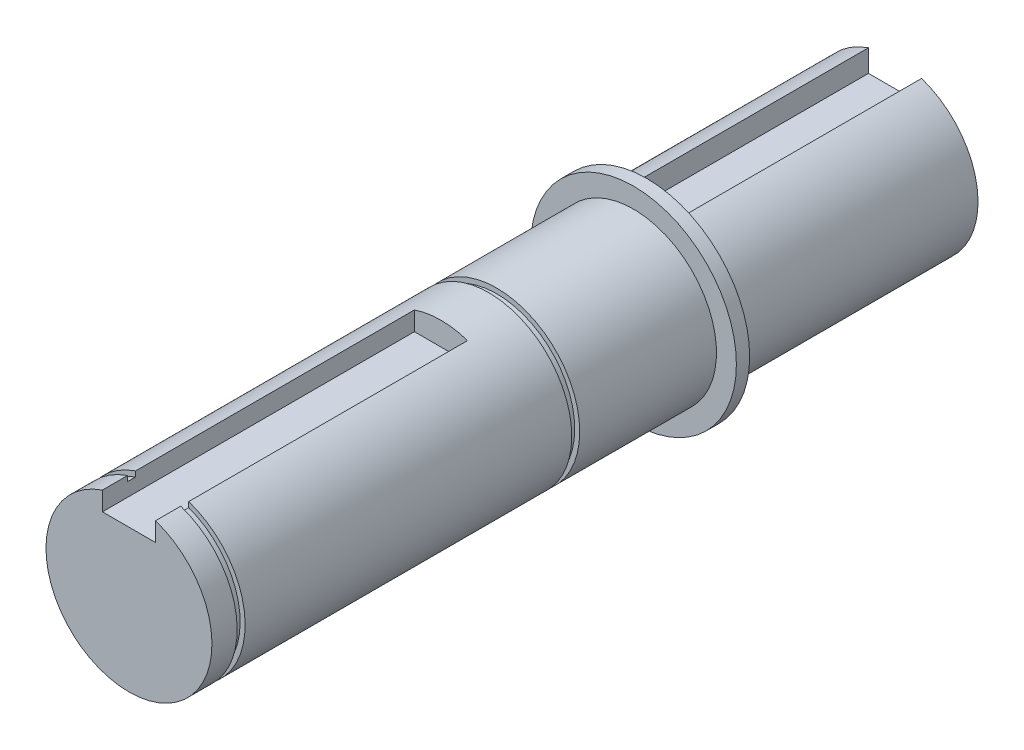
SolidWorks part; units mm, degrees
material "Plain Carbon Steel"
ref_plane "Front Plane" through (0, 0, 0) normal (0, 0, 1) x (1, 0, 0)
ref_plane "Top Plane" through (0, 0, 0) normal (0, 1, 0) x (1, 0, 0)
ref_plane "Right Plane" through (0, 0, 0) normal (1, 0, 0) x (0, 0, -1)
sketch "Sketch1" plane through (0, 0, 0) normal (0, 0, 1) x (1, 0, 0)
  circle A0 centre (0, 0) radius 12.5
  dimension "D1" = 25
extrude "Boss-Extrude1" add sketch "Sketch1" along normal blind 115.4
sketch "Sketch4" plane through (0, 0, 0) normal (0, 0, -1) x (-1, 0, 0)
  line L0 (0, 17.05) -> (0, -17.05) construction
  line L1 (-4, 8.5) -> (4, 8.5)
  line L2 (-4, 8.5) -> (-4, 16.5)
  line L3 (-4, 16.5) -> (4, 16.5)
  line L4 (4, 8.5) -> (4, 16.5)
  line L5 (-4, 8.5) -> (4, 16.5) construction
  line L6 (-4, 16.5) -> (4, 8.5) construction
  circle A0 centre (0, 0) radius 12.5 construction
  point P0 (0, 12.5)
  dimension "D1" = 8
  dimension "D2" = 8
extrude "Cut-Extrude1" cut sketch "Sketch4" against normal blind 35.4
ref_plane "Plane1" through (0, 0, 37.4) normal (0, 0, -1) x (-1, 0, 0)
sketch "Sketch11" plane through (0, 0, 37.4) normal (0, 0, -1) x (-1, 0, 0)
  circle A0 centre (0, 0) radius 15.5
  dimension "D1" = 31
extrude "Boss-Extrude4" add sketch "Sketch11" against normal blind 2
ref_plane "Plane2" through (0, 0, 60) normal (0, 0, 1) x (1, 0, 0)
sketch "Sketch12" plane through (0, 0, 60) normal (0, 0, 1) x (1, 0, 0)
  circle A0 centre (0, 0) radius 12.5
  circle A1 centre (0, 0) radius 11.75
  dimension "D1" = 25
  dimension "D2" = 23.5
extrude "Cut-Extrude2" cut sketch "Sketch12" along normal blind 1.2
sketch "Sketch13" plane through (0, 0, 115.4) normal (0, 0, 1) x (1, 0, 0)
  line L1 (-4, 9) -> (4, 9)
  line L2 (-4, 9) -> (-4, 16)
  line L3 (-4, 16) -> (4, 16)
  line L4 (4, 9) -> (4, 16)
  line L5 (-4, 9) -> (4, 16) construction
  line L6 (-4, 16) -> (4, 9) construction
  circle A0 centre (0, 0) radius 12.5 construction
  point P0 (0, 12.5)
  dimension "D1" = 8
  dimension "D2" = 7
extrude "Cut-Extrude3" cut sketch "Sketch13" against normal blind 47
ref_plane "Plane4" through (0, 0, 110.4) normal (0, 0, 1) x (1, 0, 0)
sketch "Sketch16" plane through (0, 0, 110.4) normal (0, 0, 1) x (1, 0, 0)
  circle A0 centre (0, 0) radius 12.5
  circle A1 centre (0, 0) radius 11.75
  dimension "D1" = 25
  dimension "D2" = 23.5
extrude "Cut-Extrude5" cut sketch "Sketch16" along normal blind 1.2 contours A1 | A0
